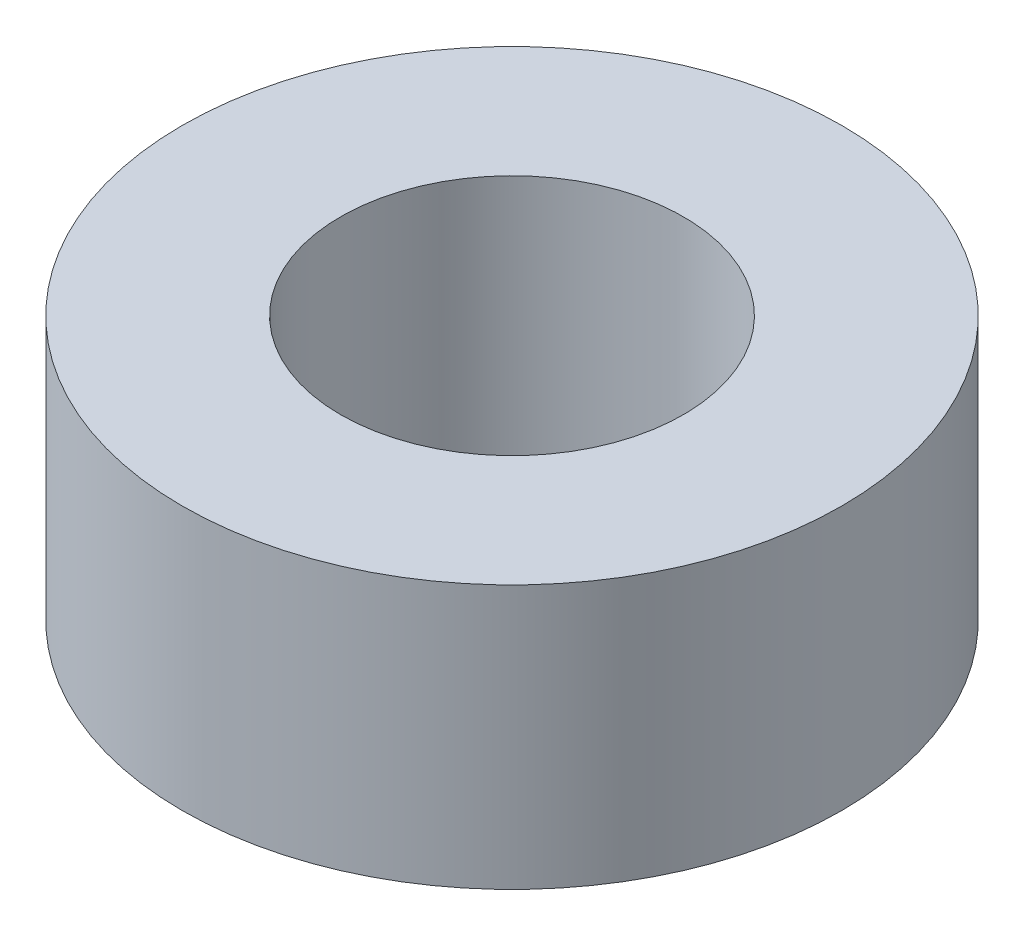
SolidWorks part; units mm, degrees
ref_plane "Front Plane" through (0, 0, 0) normal (0, 0, 1) x (1, 0, 0)
ref_plane "Top Plane" through (0, 0, 0) normal (0, 1, 0) x (1, 0, 0)
ref_plane "Right Plane" through (0, 0, 0) normal (1, 0, 0) x (0, 0, -1)
sketch "Sketch1" plane through (0, 0, 0) normal (0, 1, 0) x (1, 0, 0)
  circle A0 centre (0, 0) radius 6.35
  circle A1 centre (0, 0) radius 3.302
  dimension "D1" = 6.604
  dimension "D2" = 12.7
extrude "Boss-Extrude1" add sketch "Sketch1" along normal blind 5.08
